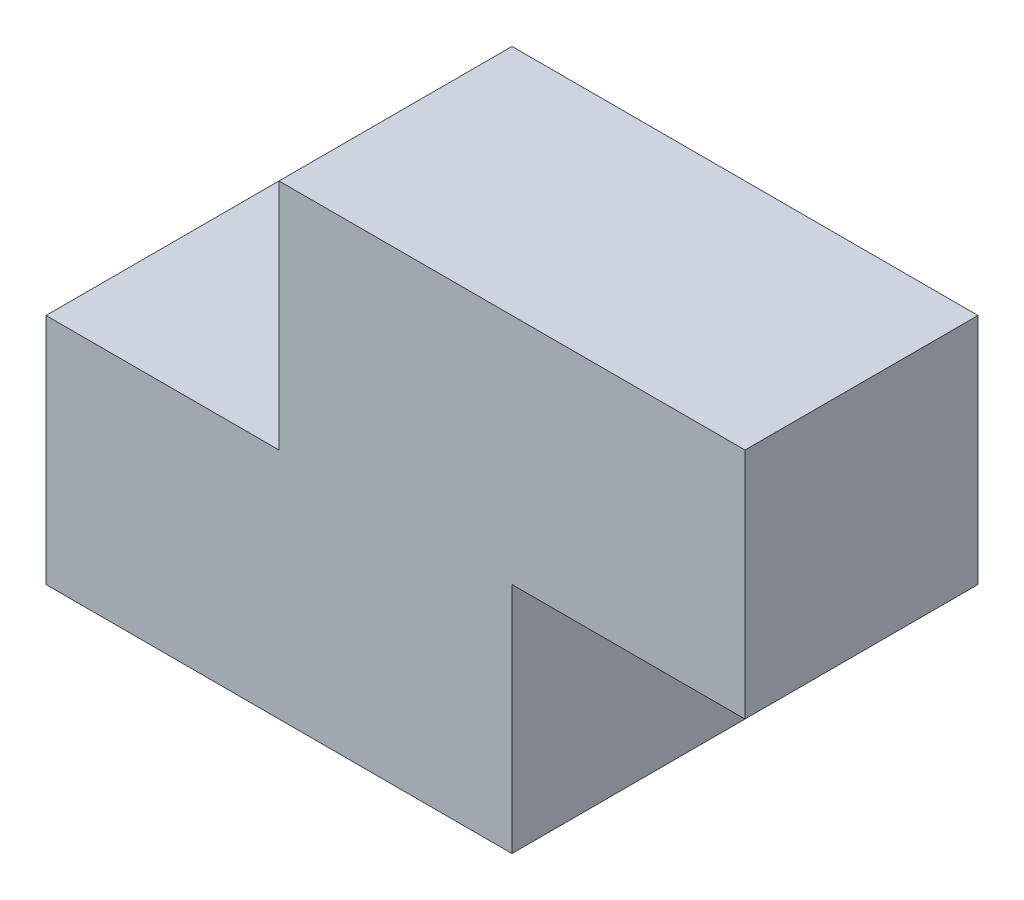
SolidWorks part; units mm, degrees
ref_plane "Front Plane" through (0, 0, 0) normal (0, 0, 1) x (1, 0, 0)
ref_plane "Top Plane" through (0, 0, 0) normal (0, 1, 0) x (1, 0, 0)
ref_plane "Right Plane" through (0, 0, 0) normal (1, 0, 0) x (0, 0, -1)
sketch "Sketch1" plane through (0, 0, 0) normal (0, 0, 1) x (1, 0, 0)
  line L0 (-89.2105, 0) -> (81.3158, 0) construction
  line L1 (0, 80.0457) -> (0, -52.4013) construction
  line L2 (-30, 0) -> (30, 0)
  line L3 (30, 0) -> (30, 30)
  line L4 (30, 30) -> (60, 30)
  line L5 (60, 30) -> (60, 60)
  line L6 (60, 60) -> (0, 60)
  line L7 (0, 60) -> (0, 30)
  line L8 (0, 30) -> (-30, 30)
  line L9 (-30, 30) -> (-30, 0)
  point P13 (0, 80.0457)
  dimension "D1" = 30
  dimension "D2" = 30
  dimension "D3" = 60
  dimension "D4" = 60
  dimension "D5" = 90
extrude "Boss-Extrude1" add sketch "Sketch1" against normal blind 30
